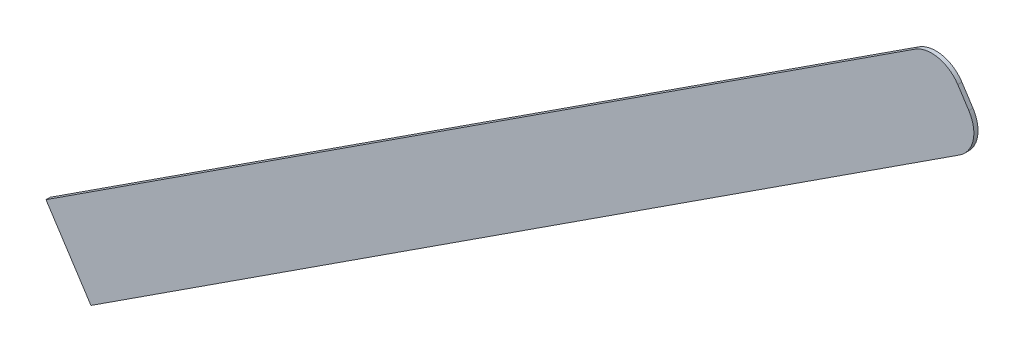
SolidWorks part; units mm, degrees
ref_plane "Front Plane" through (0, 0, 0) normal (0, 0, 1) x (1, 0, 0)
ref_plane "Top Plane" through (0, 0, 0) normal (0, 1, 0) x (1, 0, 0)
ref_plane "Right Plane" through (0, 0, 0) normal (1, 0, 0) x (0, 0, -1)
sketch "Sketch2" plane through (0, 0, 0) normal (0, 0, 1) x (1, 0, 0)
  line L0 (-347.9278, -207.1501) -> (-326.2372, -240.5201)
  line L1 (-347.9278, -207.1501) -> (71.294, 65.3441)
  line L2 (-326.2372, -240.5201) -> (92.9846, 31.974)
  line L3 (92.0455, 60.9423) -> (97.3864, 52.7255)
  arc A0 (71.294, 65.3441) -> (92.0455, 60.9423) centre (79.4689, 52.7674) cw
  arc A1 (92.9846, 31.974) -> (97.3864, 52.7255) centre (84.8097, 44.5507) ccw
  dimension "D1" = 15
  dimension "D2" = 500
extrude "Boss-Extrude1" add sketch "Sketch2" along normal blind 2
